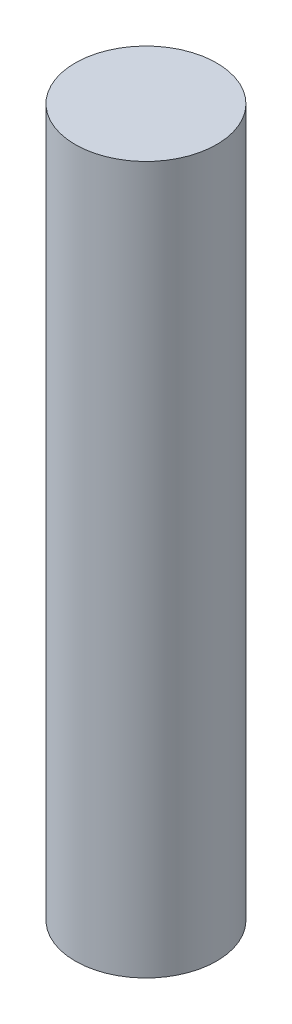
SolidWorks part; units mm, degrees
ref_plane "Front Plane" through (0, 0, 0) normal (0, 0, 1) x (1, 0, 0)
ref_plane "Top Plane" through (0, 0, 0) normal (0, 1, 0) x (1, 0, 0)
ref_plane "Right Plane" through (0, 0, 0) normal (1, 0, 0) x (0, 0, -1)
sketch "Sketch1" plane through (0, 0, 0) normal (0, 1, 0) x (1, 0, 0)
  circle A0 centre (0, 0) radius 45
  dimension "D1" = 90
extrude "Boss-Extrude1" add sketch "Sketch1" along normal blind 450 contours A0
sketch "Sketch2" plane through (0, 450, 0) normal (0, 1, 0) x (1, 0, 0)
  circle A0 centre (0, 0) radius 35
